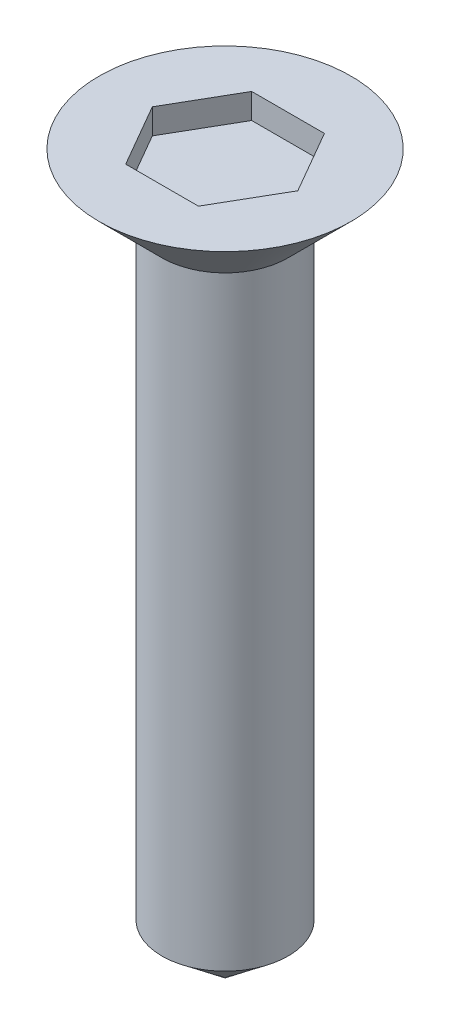
SolidWorks part; units mm, degrees
ref_plane "Alzado" through (0, 0, 0) normal (0, 0, 1) x (1, 0, 0)
ref_plane "Planta" through (0, 0, 0) normal (0, 1, 0) x (1, 0, 0)
ref_plane "Vista lateral" through (0, 0, 0) normal (1, 0, 0) x (0, 0, -1)
sketch "Croquis1" plane through (0, 0, 0) normal (0, 1, 0) x (1, 0, 0)
  circle A0 centre (0, 0) radius 1.25
  dimension "D1" = 2.5
extrude "Saliente-Extruir1" add sketch "Croquis1" along normal blind 12
sketch "Croquis2" plane through (0, 0, 0) normal (1, 0, 0) x (0, 0, -1)
  line L0 (-1.25, 12) -> (-2.5, 13.25)
  line L1 (-2.5, 13.25) -> (2.5, 13.25)
  line L2 (2.5, 13.25) -> (1.25, 12)
  line L3 (1.25, 12) -> (-1.25, 12)
  line L4 (0, 13.25) -> (0, 12) construction
  point P6 (0, 13.25)
  point P7 (0, 12)
  dimension "D1" = 5
  dimension "D2" = 90
revolve "Revolución1" add sketch "Croquis2" angle 360 about L4
sketch "Croquis3" plane through (0, 13.25, 0) normal (0, 1, 0) x (1, 0, 0)
  line L1 (1.4434, 0) -> (0.7217, 1.25)
  line L2 (0.7217, 1.25) -> (-0.7217, 1.25)
  line L3 (-0.7217, 1.25) -> (-1.4434, 0)
  line L4 (-1.4434, 0) -> (-0.7217, -1.25)
  line L5 (-0.7217, -1.25) -> (0.7217, -1.25)
  line L6 (0.7217, -1.25) -> (1.4434, 0)
  circle A0 centre (0, 0) radius 1.25 construction
  dimension "D1" = 2.5
extrude "Cortar-Extruir1" cut sketch "Croquis3" against normal blind 0.5
sketch "Croquis4" plane through (0, 0, 0) normal (0, 0, 1) x (1, 0, 0)
  line L0 (-1.25, 0) -> (0, -1)
  line L1 (0, -1) -> (1.25, 0)
  line L2 (1.25, 0) -> (-1.25, 0)
  line L3 (0, 0) -> (0, -1) construction
  dimension "D1" = 1
revolve "Revolución2" add sketch "Croquis4" angle 360 about L3
